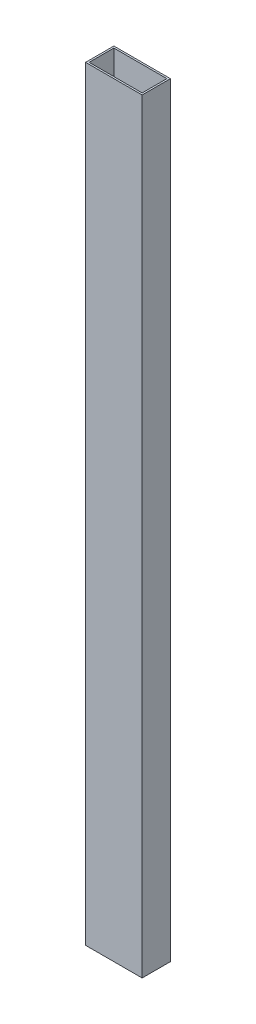
SolidWorks part; units mm, degrees
ref_plane "Front Plane" through (0, 0, 0) normal (0, 0, 1) x (1, 0, 0)
ref_plane "Top Plane" through (0, 0, 0) normal (0, 1, 0) x (1, 0, 0)
ref_plane "Right Plane" through (0, 0, 0) normal (1, 0, 0) x (0, 0, -1)
sketch "Sketch1" plane through (0, 0, 0) normal (0, 1, 0) x (1, 0, 0)
  line L1 (-13.1274, 4.8541) -> (37.6726, 4.8541)
  line L2 (-13.1274, 4.8541) -> (-13.1274, -20.5459)
  line L3 (-13.1274, -20.5459) -> (37.6726, -20.5459)
  line L4 (37.6726, 4.8541) -> (37.6726, -20.5459)
  line L5 (-11.5399, 3.2666) -> (36.0851, 3.2666)
  line L6 (-11.5399, 3.2666) -> (-11.5399, -18.9584)
  line L7 (-11.5399, -18.9584) -> (36.0851, -18.9584)
  line L8 (36.0851, 3.2666) -> (36.0851, -18.9584)
  dimension "D1" = 1.5875
  dimension "D2" = 1.5875
  dimension "D3" = 1.5875
  dimension "D4" = 1.5875
  dimension "D5" = 50.8
  dimension "D6" = 25.4
extrude "Boss-Extrude1" add sketch "Sketch1" along normal blind 687.07
